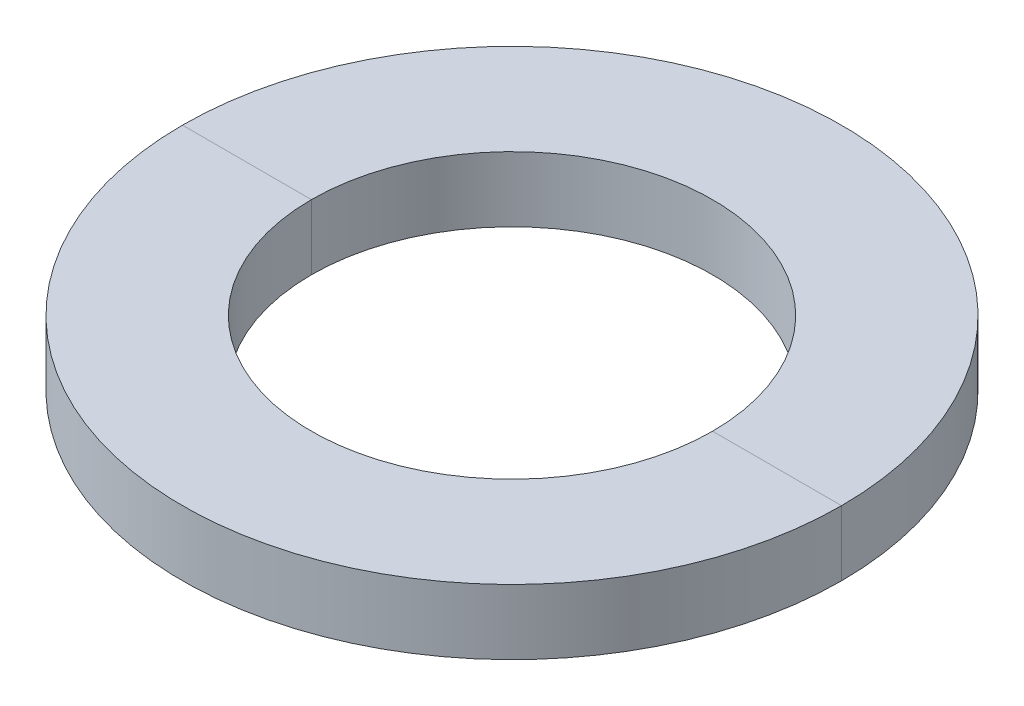
SolidWorks part; units mm, degrees
ref_plane "Front Plane" through (0, 0, 0) normal (0, 0, 1) x (1, 0, 0)
ref_plane "Top Plane" through (0, 0, 0) normal (0, 1, 0) x (1, 0, 0)
ref_plane "Right Plane" through (0, 0, 0) normal (1, 0, 0) x (0, 0, -1)
sketch "Sketch1" plane through (0, 0, 0) normal (0, 1, 0) x (1, 0, 0)
  circle A0 centre (0, 0) radius 18.2562
  circle A1 centre (0, 0) radius 11.1125
  dimension "D1" = 22.225
  dimension "D2" = 36.5125
extrude "Extrude1" add sketch "Sketch1" along normal blind 3.6068
split "Split1" trim tools "Front Plane" resulting bodies 102 103
